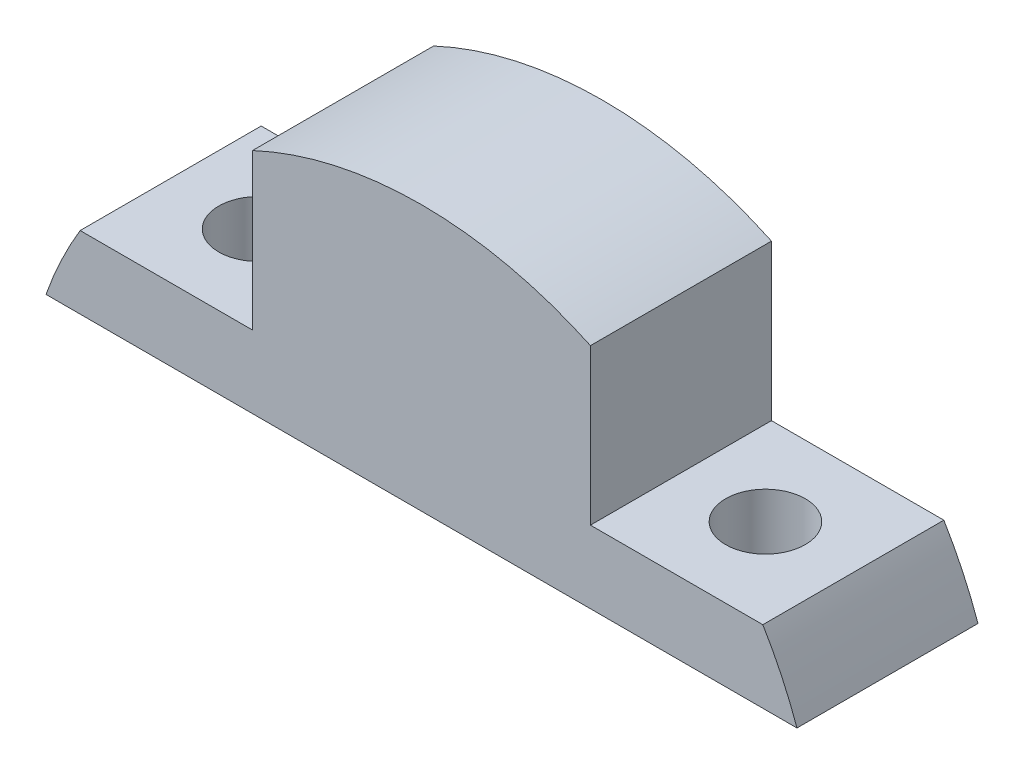
SolidWorks part; units mm, degrees
ref_plane "정면" through (0, 0, 0) normal (0, 0, 1) x (1, 0, 0)
ref_plane "윗면" through (0, 0, 0) normal (0, 1, 0) x (1, 0, 0)
ref_plane "우측면" through (0, 0, 0) normal (1, 0, 0) x (0, 0, -1)
sketch "스케치1" plane through (0, 0, 0) normal (0, 0, 1) x (1, 0, 0)
  line L0 (0, 36.3895) -> (0, -24.0799) construction
  line L1 (-14, 22) -> (14, 22)
  line L2 (-40, 6) -> (-40, 0)
  line L3 (-40, 0) -> (40, 0)
  line L4 (40, 6) -> (40, 0)
  line L7 (40, 6) -> (14, 6)
  line L8 (14, 22) -> (14, 6)
  line L9 (-14, 22) -> (-14, 6)
  line L10 (-40, 6) -> (-14, 6)
  dimension "D1" = 22
  dimension "D2" = 6
  dimension "D3" = 80
  dimension "D4" = 14
extrude "보스-돌출1" add sketch "스케치1" along normal mid plane 15
sketch "스케치2" plane through (0, 0, 0) normal (0, 0, 1) x (1, 0, 0)
  line L0 (14, 22) -> (-14, 22) construction
  line L1 (0, 0) -> (0, 34.7812) construction
  line L2 (-40, 0) -> (-31.1127, 0)
  line L3 (-40, 0) -> (40, 0) construction
  line L4 (-40, 6) -> (-40, 0) construction
  line L5 (-40, 0) -> (-40, 32)
  line L6 (-40, 32) -> (40, 32)
  line L7 (40, 32) -> (40, 0)
  line L8 (40, 0) -> (31.1127, 0)
  line L9 (40, 0) -> (40, 6) construction
  arc A0 (31.1127, 0) -> (-31.1127, 0) centre (0, -11) ccw
  dimension "D1" = 66
  dimension "D2" = 10
extrude "컷-돌출3" cut sketch "스케치2" against normal through all both and the other way through all
hole_wizard "M4 여유 구멍1" positions "스케치3" profile "스케치4" hole size "M4" standard "KS" end condition through all
sketch "스케치3" plane through (0, 6, 0) normal (0, 1, 0) x (1, 0, 0)
  line L0 (-14, -7.5) -> (-28.2843, -7.5) construction
  line L1 (28.2843, -7.5) -> (14, -7.5) construction
  point P0 (-21, 0)
  point P2 (21, 0)
  dimension "D1" = 21
  dimension "D2" = 21
  dimension "D3" = 7.5
  dimension "D4" = 7.5
sketch "스케치4" plane through (-21, 6, 0) normal (1, 0, 0) x (0, 0, 1)
  line L0 (0, 0) -> (0, 6)
  line L1 (0, 6) -> (3.3, 6)
  line L2 (3.3, 6) -> (3.3, 0)
  line L5 (3.3, 0) -> (0, 0)
  line L11 (0, -6.35) -> (0, 107.95) construction
  dimension "관통 구멍 지름" = 6.6
  dimension "관통 구멍 깊이" = 6
